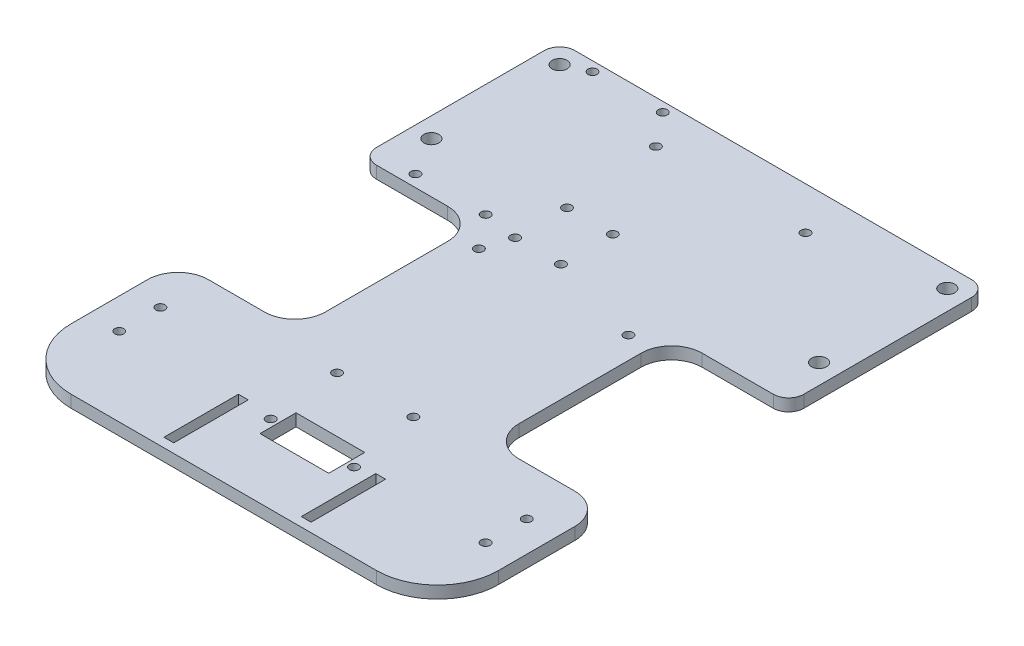
SolidWorks part; units mm, degrees
ref_plane "Front Plane" through (0, 0, 0) normal (0, 0, 1) x (1, 0, 0)
ref_plane "Top Plane" through (0, 0, 0) normal (0, 1, 0) x (1, 0, 0)
ref_plane "Right Plane" through (0, 0, 0) normal (1, 0, 0) x (0, 0, -1)
sketch "Sketch1" plane through (0, 0, 0) normal (0, 1, 0) x (1, 0, 0)
  line L0 (-120, 0) -> (-135, 0)
  line L19 (-20, 0) -> (-120, 0)
  line L20 (0, -20) -> (0, -160)
  line L21 (-20, -180) -> (-120, -180)
  line L22 (-140, -20) -> (-140, -160)
  line L23 (-140, -5) -> (-140, -20)
  line L24 (-20, 0) -> (-5, 0)
  line L25 (0, -5) -> (0, -20)
  arc A27 (-120, -180) -> (-140, -160) centre (-120, -160) cw
  arc A28 (0, -160) -> (-20, -180) centre (-20, -160) cw
  arc A31 (-5, 0) -> (0, -5) centre (-5, -5) cw
  arc A32 (-135, 0) -> (-140, -5) centre (-135, -5) ccw
  point P9 (0, -180)
  point P12 (0, 0)
  point P15 (-140, 0)
  point P17 (0, 0)
  point P20 (-140, 0)
  dimension "D1" = 140
  dimension "D2" = 180
  dimension "D4" = 5
  dimension "D3" = 20
extrude "Boss-Extrude1" add sketch "Sketch1" along normal blind 4
sketch "Sketch2" plane through (0, 4, 0) normal (0, 1, 0) x (1, 0, 0)
  line L0 (-70, 0) -> (-70, -53.3557) construction
  line L1 (-77.9, -148.4297) -> (-55.4, -148.4297)
  line L2 (-77.9, -148.4297) -> (-77.9, -160.2297)
  line L3 (-77.9, -160.2297) -> (-55.4, -160.2297)
  line L4 (-55.4, -148.4297) -> (-55.4, -160.2297)
  line L5 (-5, 0) -> (-135, 0) construction
  line L6 (-91, -152.5963) -> (-91, -177) construction
  line L7 (-92.6, -152.5963) -> (-89.4, -152.5963)
  line L8 (-92.6, -152.5963) -> (-92.6, -177)
  line L9 (-92.6, -177) -> (-89.4, -177)
  line L10 (-89.4, -152.5963) -> (-89.4, -177)
  line L11 (-120, -180) -> (-20, -180) construction
  line L12 (-46, -152.5963) -> (-46, -177) construction
  line L13 (-47.6, -152.5963) -> (-44.4, -152.5963)
  line L14 (-47.6, -152.5963) -> (-47.6, -177)
  line L15 (-47.6, -177) -> (-44.4, -177)
  line L16 (-44.4, -152.5963) -> (-44.4, -177)
  circle A0 centre (-80.3, -154.3297) radius 1.5
  circle A1 centre (-53, -154.3297) radius 1.5
  circle A4 centre (-6.5, -6.5) radius 2.45
  circle A5 centre (-6.5, -48.5) radius 2.45
  circle A6 centre (-133.5, -48.5) radius 2.45
  circle A7 centre (-133.5, -6.5) radius 2.45
  circle A24 centre (-82.507, -130.3882) radius 1.5
  circle A25 centre (-57.507, -130.3882) radius 1.5
  circle A28 centre (-76.6761, -45.8956) radius 1.5
  circle A29 centre (-91.6761, -45.8956) radius 1.5
  circle A30 centre (-76.6761, -62.8956) radius 1.5
  circle A31 centre (-91.6761, -62.8956) radius 1.5
  circle A32 centre (-94.5, -71.9482) radius 1.5
  circle A33 centre (-45.5, -71.9482) radius 1.5
  circle A34 centre (-94.5, -13.9482) radius 1.5
  circle A35 centre (-45.5, -13.9482) radius 1.5
  circle A38 centre (-126.0818, -3.1354) radius 1.5
  circle A39 centre (-103.0818, -3.1354) radius 1.5
  circle A40 centre (-126.0818, -61.1354) radius 1.5
  circle A41 centre (-103.0818, -61.1354) radius 1.5
  circle A42 centre (-130, -140.75) radius 1.5
  circle A43 centre (-130, -154.25) radius 1.5
  circle A44 centre (-10, -154.25) radius 1.5
  circle A45 centre (-10, -140.75) radius 1.5
  circle A46 centre (-91, -154.499) radius 1.5 construction
  circle A47 centre (-46, -154.499) radius 1.5 construction
  point P66 (0, 0)
  dimension "D1" = 3
  dimension "D2" = 3
  dimension "D3" = 3
  dimension "D4" = 3.2
  dimension "D5" = 3
  dimension "D6" = 24.4037
  dimension "D7" = 24.4037
  dimension "D8" = 3.2
extrude "Cut-Extrude1" cut sketch "Sketch2" against normal through all both and the other way through all
sketch "Sketch3" plane through (0, 0, 0) normal (0, -1, 0) x (-1, 0, 0)
  line L0 (0, -160) -> (0, -5) construction
  line L1 (0, -65) -> (28.307, -65)
  line L2 (0, -65) -> (0, -125)
  line L3 (0, -125) -> (28.307, -125)
  line L4 (38.307, -75) -> (38.307, -115)
  line L5 (70, 0) -> (70, -19.6212) construction
  line L6 (5, 0) -> (135, 0) construction
  line L7 (140, -65) -> (140, -125)
  line L8 (140, -65) -> (111.693, -65)
  line L9 (101.693, -75) -> (101.693, -115)
  line L10 (140, -125) -> (111.693, -125)
  arc A0 (28.307, -125) -> (38.307, -115) centre (28.307, -115) ccw
  arc A1 (28.307, -65) -> (38.307, -75) centre (28.307, -75) cw
  arc A2 (111.693, -65) -> (101.693, -75) centre (111.693, -75) ccw
  arc A3 (111.693, -125) -> (101.693, -115) centre (111.693, -115) cw
  dimension "D1" = 10
  dimension "D2" = 60
  dimension "D3" = 65
extrude "Cut-Extrude2" cut sketch "Sketch3" against normal through all both and the other way through all
fillet "Fillet1" radius 10 2 edges at (0, 2, 125) (-140, 2, 125)
fillet "Fillet2" radius 5 2 edges at (-140, 2, 65) (0, 2, 65)
